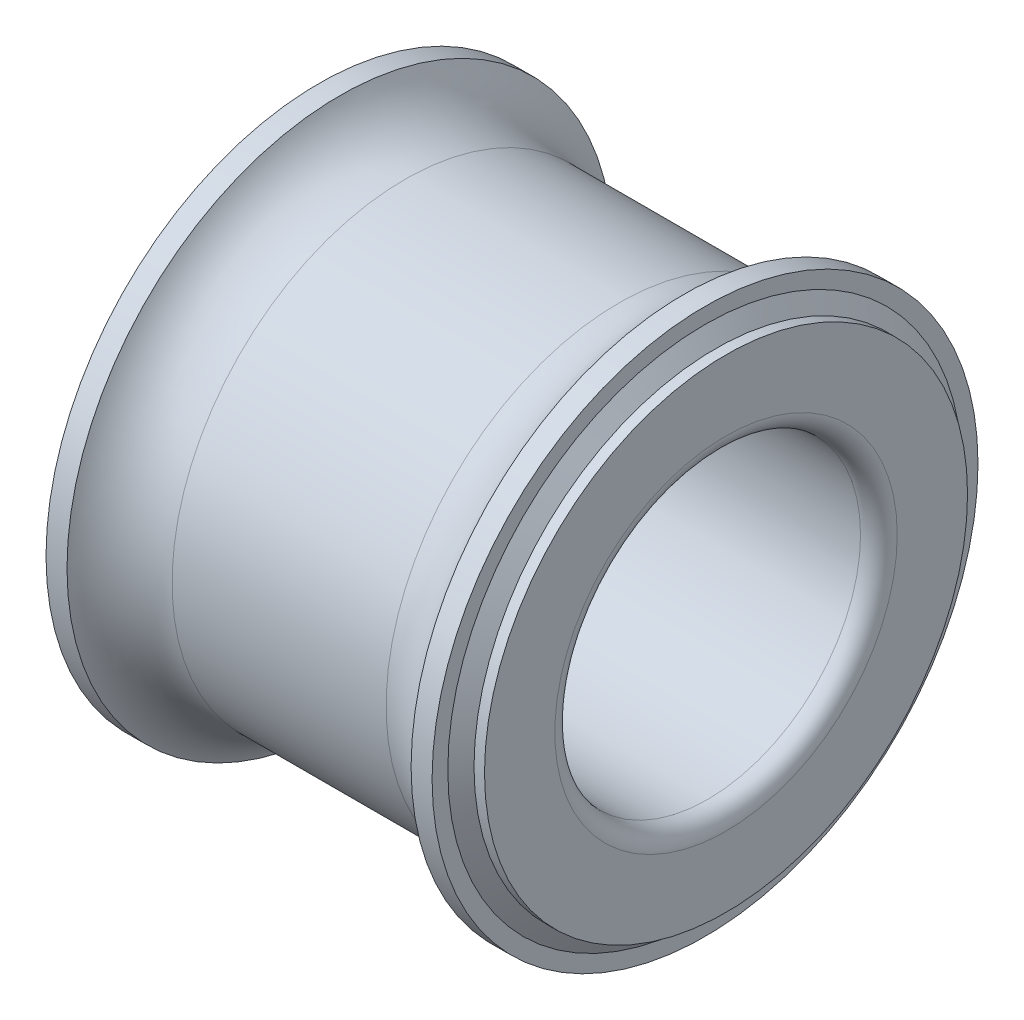
SolidWorks part; units mm, degrees
ref_plane "Front Plane" through (0, 0, 0) normal (0, 0, 1) x (1, 0, 0)
ref_plane "Top Plane" through (0, 0, 0) normal (0, 1, 0) x (1, 0, 0)
ref_plane "Right Plane" through (0, 0, 0) normal (1, 0, 0) x (0, 0, -1)
ref_plane "Plane1" through (0, 0, 0) normal (0, 0, 1) x (1, 0, 0)
sketch "Sketch1" plane through (0, 0, 0) normal (0, 0, 1) x (1, 0, 0)
  line L0 (0.6, 5) -> (13.4, 5)
  line L1 (14, 5.6) -> (14, 8.728)
  line L2 (13.8, 8.928) -> (12.6271, 8.928)
  line L3 (10.5, 7.618) -> (3.5, 7.618)
  line L4 (1.3729, 8.928) -> (0.2, 8.928)
  line L5 (0, 8.728) -> (0, 5.6)
  line L6 (13.4, 0) -> (0.6, 0) construction
  arc A0 (0, 5.6) -> (0.6, 5) centre (0.6, 5.6) ccw
  arc A1 (13.4, 5) -> (14, 5.6) centre (13.4, 5.6) ccw
  arc A2 (14, 8.728) -> (13.8, 8.928) centre (13.8, 8.728) ccw
  arc A3 (12.6271, 8.928) -> (10.5, 7.618) centre (10.5, 10) cw
  arc A4 (3.5, 7.618) -> (1.3729, 8.928) centre (3.5, 10) cw
  arc A5 (0.2, 8.928) -> (0, 8.728) centre (0.2, 8.728) ccw
revolve "Revolve1" add sketch "Sketch1" angle 360 about L6
ref_plane "Plane2" through (0, 0, 0) normal (0, 0, 1) x (1, 0, 0)
sketch "Sketch2" plane through (0, 0, 0) normal (0, 0, 1) x (1, 0, 0)
  line L0 (0, 7.9) -> (0.3432, 7.9)
  line L1 (0.3432, 7.9) -> (0.6864, 8.414)
  line L2 (0.6864, 8.414) -> (0.6864, 8.928)
  line L3 (0.6864, 8.928) -> (13.3136, 8.928)
  line L4 (13.3136, 8.928) -> (13.3136, 8.414)
  line L5 (13.3136, 8.414) -> (13.6568, 7.9)
  line L6 (13.6568, 7.9) -> (14, 7.9)
  line L7 (14, 7.9) -> (14, 11.828)
  line L8 (14, 11.828) -> (0, 11.828)
  line L9 (0, 11.828) -> (0, 7.9)
  line L10 (14, 0) -> (0, 0) construction
revolve "Cut-Revolve1" cut sketch "Sketch2" angle 360 about L10
